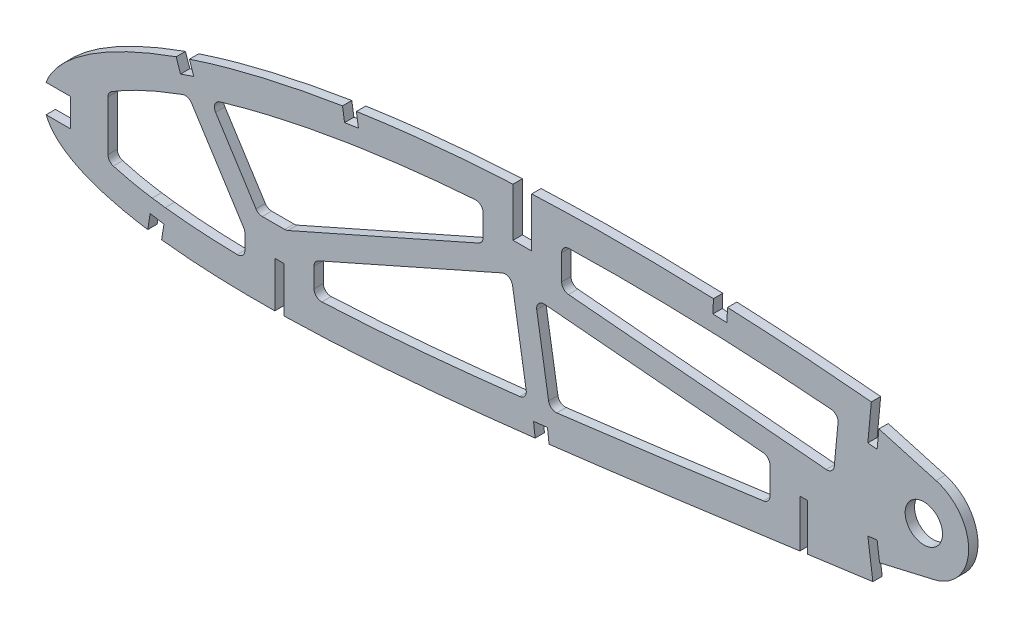
SolidWorks part; units mm, degrees
material "Plywood"
ref_plane "Front Plane" through (0, 0, 0) normal (0, 0, 1) x (1, 0, 0)
ref_plane "Top Plane" through (0, 0, 0) normal (0, 1, 0) x (1, 0, 0)
ref_plane "Right Plane" through (0, 0, 0) normal (1, 0, 0) x (0, 0, -1)
curve "Curve1"
  spline degree 3 poles (452.1031, 0.7048, 0) (452.0685, 0.7262, 0) (451.9301, 0.8117, 0) (451.6183, 1.003, 0) (451.099, 1.3216, 0) (450.372, 1.7653, 0) (449.438, 2.3329, 0) (448.2963, 3.0204, 0) (446.9478, 3.8257, 0) (445.3928, 4.7448, 0) (443.6314, 5.7736, 0) (441.6643, 6.9077, 0) (439.4916, 8.1409, 0) (437.1143, 9.468, 0) (434.5331, 10.8828, 0) (431.7485, 12.3789, 0) (428.7615, 13.9486, 0) (425.5733, 15.5853, 0) (422.1844, 17.2798, 0) (418.5964, 19.0251, 0) (414.8106, 20.8125, 0) (410.8282, 22.6325, 0) (406.6515, 24.4776, 0) (402.2816, 26.3365, 0) (397.7212, 28.201, 0) (392.972, 30.0605, 0) (388.0369, 31.9065, 0) (382.9178, 33.7272, 0) (377.6186, 35.5144, 0) (372.1418, 37.2567, 0) (366.4913, 38.9446, 0) (360.6704, 40.5671, 0) (354.684, 42.1159, 0) (348.5359, 43.5797, 0) (342.2312, 44.9487, 0) (335.775, 46.2147, 0) (329.1727, 47.3651, 0) (322.4425, 48.3989, 0) (315.6929, 49.2588, 0) (308.9571, 50.1023, 0) (302.2314, 50.8946, 0) (295.4235, 51.6533, 0) (288.5399, 52.3742, 0) (281.5875, 53.055, 0) (274.5733, 53.6928, 0) (267.5046, 54.2857, 0) (260.3883, 54.8303, 0) (253.2318, 55.3259, 0) (246.0422, 55.768, 0) (238.8272, 56.1563, 0) (231.5941, 56.4881, 0) (224.3504, 56.7611, 0) (217.1039, 56.9737, 0) (209.862, 57.1238, 0) (202.6326, 57.2105, 0) (195.4232, 57.2315, 0) (188.2416, 57.1863, 0) (181.0954, 57.0734, 0) (173.9924, 56.8912, 0) (166.9401, 56.6395, 0) (159.9462, 56.3182, 0) (153.0184, 55.9248, 0) (146.164, 55.4618, 0) (139.3909, 54.9271, 0) (132.7063, 54.3206, 0) (126.1174, 53.645, 0) (119.6314, 52.8983, 0) (113.2554, 52.0826, 0) (106.9962, 51.1996, 0) (100.8609, 50.2488, 0) (94.8561, 49.2329, 0) (88.9882, 48.153, 0) (83.2635, 47.0122, 0) (77.6882, 45.8109, 0) (72.2682, 44.5525, 0) (67.0092, 43.2395, 0) (61.9167, 41.874, 0) (56.9959, 40.4594, 0) (52.2519, 38.999, 0) (47.6902, 37.4943, 0) (43.3141, 35.951, 0) (39.1291, 34.3702, 0) (35.1384, 32.7568, 0) (31.3466, 31.113, 0) (27.7567, 29.4439, 0) (24.3726, 27.7512, 0) (21.1967, 26.0397, 0) (18.2324, 24.3122, 0) (15.4823, 22.5717, 0) (12.9477, 20.8227, 0) (10.632, 19.0664, 0) (8.5361, 17.307, 0) (6.6613, 15.5474, 0) (5.0102, 13.7886, 0) (3.5829, 12.0339, 0) (2.3811, 10.2847, 0) (1.4051, 8.5424, 0) (0.6571, 6.8085, 0) (0.1363, 5.084, 0) (-0.1488, 3.3712, 0) (-0.2197, 1.669, 0) (-0.0731, 0.5555, 0) (0, 0, 0) knots 0 0 0 0 0.000254 0.001015 0.002283 0.004057 0.006331 0.009105 0.012374 0.016134 0.02038 0.025106 0.030306 0.035972 0.0421 0.048678 0.055702 0.06316 0.071046 0.07935 0.088063 0.097176 0.106678 0.116562 0.126814 0.137428 0.148394 0.1597 0.171338 0.183298 0.19557 0.208144 0.221012 0.234162 0.247587 0.261277 0.275223 0.289414 0.303771 0.317689 0.331784 0.34604 0.360444 0.374983 0.38964 0.404403 0.419257 0.434187 0.449177 0.464215 0.479284 0.49437 0.509458 0.524532 0.539579 0.554583 0.56953 0.584403 0.599191 0.613877 0.628447 0.642889 0.657186 0.671326 0.685294 0.699078 0.712665 0.726043 0.739198 0.752118 0.764792 0.777208 0.789356 0.801224 0.812804 0.824083 0.835055 0.84571 0.856038 0.866034 0.875689 0.884998 0.893953 0.902553 0.910789 0.918661 0.926166 0.933303 0.940071 0.946475 0.952518 0.958205 0.963547 0.968557 0.97325 0.977651 0.981787 0.985694 0.989415 0.993001 0.996508 1 1 1 1
curve "Curve2"
  spline degree 3 poles (0, 0, 0) (0.1161, -0.5481, 0) (0.3488, -1.6467, 0) (0.9811, -3.2283, 0) (1.8173, -4.7487, 0) (2.8749, -6.2038, 0) (4.147, -7.5932, 0) (5.6306, -8.9184, 0) (7.3243, -10.1787, 0) (9.226, -11.3735, 0) (11.3328, -12.5041, 0) (13.6425, -13.5697, 0) (16.1528, -14.5701, 0) (18.8611, -15.5039, 0) (21.764, -16.3724, 0) (24.8588, -17.1737, 0) (28.1419, -17.9088, 0) (31.6103, -18.5759, 0) (35.26, -19.1755, 0) (39.0874, -19.7075, 0) (43.0885, -20.172, 0) (47.2594, -20.5682, 0) (51.596, -20.8969, 0) (56.0938, -21.1583, 0) (60.7487, -21.3533, 0) (65.556, -21.481, 0) (70.5112, -21.5436, 0) (75.6096, -21.5419, 0) (80.8464, -21.4754, 0) (86.2171, -21.3479, 0) (91.7164, -21.1586, 0) (97.3395, -20.9096, 0) (103.0813, -20.6036, 0) (108.9365, -20.2416, 0) (114.9002, -19.8251, 0) (120.967, -19.3576, 0) (127.1315, -18.8401, 0) (133.3883, -18.2757, 0) (139.7319, -17.6673, 0) (146.1567, -17.0167, 0) (152.6572, -16.327, 0) (159.2275, -15.6004, 0) (165.862, -14.8409, 0) (172.5546, -14.0497, 0) (179.2998, -13.2315, 0) (186.0911, -12.3877, 0) (192.923, -11.5217, 0) (199.7891, -10.6375, 0) (206.6832, -9.7349, 0) (213.5994, -8.8205, 0) (220.5311, -7.8935, 0) (227.4721, -6.9586, 0) (234.4161, -6.0188, 0) (241.3564, -5.0743, 0) (248.2868, -4.1291, 0) (255.2009, -3.1857, 0) (262.0918, -2.2442, 0) (268.9535, -1.3094, 0) (275.779, -0.3811, 0) (282.5619, 0.5389, 0) (289.2958, 1.4477, 0) (295.9744, 2.3443, 0) (302.5907, 3.228, 0) (309.138, 4.0992, 0) (315.5119, 4.9314, 0) (321.6955, 5.769, 0) (327.7099, 6.4556, 0) (333.6493, 7.0417, 0) (339.52, 7.5222, 0) (345.315, 7.9041, 0) (351.0275, 8.19, 0) (356.6509, 8.3839, 0) (362.1779, 8.4917, 0) (367.6017, 8.516, 0) (372.9148, 8.4647, 0) (378.1105, 8.3417, 0) (383.1813, 8.1528, 0) (388.1203, 7.9042, 0) (392.9205, 7.6027, 0) (397.5745, 7.2527, 0) (402.076, 6.8625, 0) (406.4179, 6.4377, 0) (410.5937, 5.9833, 0) (414.5972, 5.5086, 0) (418.4221, 5.0169, 0) (422.0625, 4.5163, 0) (425.5126, 4.0117, 0) (428.7669, 3.5097, 0) (431.8204, 3.015, 0) (434.6681, 2.5342, 0) (437.3055, 2.0718, 0) (439.7281, 1.6323, 0) (441.9324, 1.2212, 0) (443.9143, 0.8406, 0) (445.6709, 0.4968, 0) (447.199, 0.1913, 0) (448.4964, -0.0716, 0) (449.5609, -0.2909, 0) (450.3908, -0.463, 0) (450.9844, -0.5881, 0) (451.3411, -0.6626, 0) (451.4997, -0.6964, 0) (451.5393, -0.7048, 0) knots 0 0 0 0 0.003638 0.007293 0.011028 0.014901 0.018963 0.023258 0.027821 0.032679 0.037853 0.043362 0.049215 0.055422 0.061989 0.068918 0.076211 0.083868 0.091887 0.100266 0.109 0.118085 0.127515 0.137285 0.147388 0.157816 0.168563 0.179619 0.190977 0.202627 0.21456 0.226767 0.239236 0.251959 0.264924 0.27812 0.291536 0.30516 0.318981 0.332985 0.347163 0.361499 0.375981 0.390597 0.405333 0.420175 0.43511 0.450124 0.465203 0.480333 0.495501 0.51069 0.525887 0.541078 0.556247 0.571382 0.586466 0.601485 0.616424 0.631269 0.646007 0.660621 0.675098 0.689423 0.703582 0.716908 0.730009 0.742952 0.755726 0.76832 0.780724 0.792927 0.804916 0.816679 0.828204 0.839475 0.850481 0.861208 0.871639 0.881763 0.891564 0.901027 0.910139 0.918884 0.927249 0.935221 0.942785 0.949928 0.956638 0.962904 0.968712 0.974054 0.978918 0.983297 0.98718 0.990561 0.993433 0.995791 0.99763 0.998946 0.999737 1 1 1 1
sketch "Sketch1" plane through (0, 0, 0) normal (0, 0, 1) x (1, 0, 0)
  line L24 (452.1031, 0.7048) -> (456.094, -1.6764)
  line L25 (451.5393, -0.7048) -> (456.094, -1.6764)
  spline S2 degree 3 poles (-2902.3793, -755.52) (63.6454, 63.6466) (-7.9338, 19.0709) (0.9811, -3.2283) (1.8173, -4.7487) (2.8749, -6.2038) (4.147, -7.5932) (5.6306, -8.9184) (7.3243, -10.1787) (9.226, -11.3735) (11.3328, -12.5041) (13.6425, -13.5697) (16.1528, -14.5701) (18.8611, -15.5039) (21.764, -16.3724) (24.8588, -17.1737) (28.1419, -17.9088) (31.6103, -18.5759) (35.26, -19.1755) (39.0874, -19.7075) (43.0885, -20.172) (47.2594, -20.5682) (51.596, -20.8969) (56.0938, -21.1583) (60.7487, -21.3533) (65.556, -21.481) (70.5112, -21.5436) (75.6096, -21.5419) (80.8464, -21.4754) (86.2171, -21.3479) (91.7164, -21.1586) (97.3395, -20.9096) (103.0813, -20.6036) (108.9365, -20.2416) (114.9002, -19.8251) (120.967, -19.3576) (127.1315, -18.8401) (133.3883, -18.2757) (139.7319, -17.6673) (146.1567, -17.0167) (152.6572, -16.327) (159.2275, -15.6004) (165.862, -14.8409) (172.5546, -14.0497) (179.2998, -13.2315) (186.0911, -12.3877) (192.923, -11.5217) (199.7891, -10.6375) (206.6832, -9.7349) (213.5994, -8.8205) (220.5311, -7.8935) (227.4721, -6.9586) (234.4161, -6.0188) (241.3564, -5.0743) (248.2868, -4.1291) (255.2009, -3.1857) (262.0918, -2.2442) (268.9535, -1.3094) (275.779, -0.3811) (282.5619, 0.5389) (289.2958, 1.4477) (295.9744, 2.3443) (302.5907, 3.228) (309.138, 4.0992) (315.5119, 4.9314) (321.6955, 5.769) (327.7099, 6.4556) (333.6493, 7.0417) (339.52, 7.5222) (345.315, 7.9041) (351.0275, 8.19) (356.6509, 8.3839) (362.1779, 8.4917) (367.6017, 8.516) (372.9148, 8.4647) (378.1105, 8.3417) (383.1813, 8.1528) (388.1203, 7.9042) (392.9205, 7.6027) (397.5745, 7.2527) (402.076, 6.8625) (406.4179, 6.4377) (410.5937, 5.9833) (414.5972, 5.5086) (418.4221, 5.0169) (422.0625, 4.5163) (425.5126, 4.0117) (428.7669, 3.5097) (431.8204, 3.015) (434.6681, 2.5342) (437.3055, 2.0718) (439.7281, 1.6323) (441.9324, 1.2212) (443.9143, 0.8406) (445.6709, 0.4968) (447.199, 0.1913) (448.4964, -0.0716) (449.5609, -0.2909) (450.3908, -0.463) (450.9844, -0.5881) (467.4773, -4.0305) (482.2176, -14.7818) (1120.3699, 2922.8002) knots -0.14446 -0.14446 -0.14446 -0.14446 0.003638 0.007293 0.011028 0.014901 0.018963 0.023258 0.027821 0.032679 0.037853 0.043362 0.049215 0.055422 0.061989 0.068918 0.076211 0.083868 0.091887 0.100266 0.109 0.118085 0.127515 0.137285 0.147388 0.157816 0.168563 0.179619 0.190977 0.202627 0.21456 0.226767 0.239236 0.251959 0.264924 0.27812 0.291536 0.30516 0.318981 0.332985 0.347163 0.361499 0.375981 0.390597 0.405333 0.420175 0.43511 0.450124 0.465203 0.480333 0.495501 0.51069 0.525887 0.541078 0.556247 0.571382 0.586466 0.601485 0.616424 0.631269 0.646007 0.660621 0.675098 0.689423 0.703582 0.716908 0.730009 0.742952 0.755726 0.76832 0.780724 0.792927 0.804916 0.816679 0.828204 0.839475 0.850481 0.861208 0.871639 0.881763 0.891564 0.901027 0.910139 0.918884 0.927249 0.935221 0.942785 0.949928 0.956638 0.962904 0.968712 0.974054 0.978918 0.983297 0.98718 0.990561 0.993433 0.995791 0.99763 0.998946 0.999737 1.107215 1.107215 1.107215 1.107215 only from (0, 0) to (451.5393, -0.7048) construction
  spline S3 degree 3 poles (2072.0463, 2524.7843) (479.969, -24.2918) (467.6474, -8.829) (451.6183, 1.003) (451.099, 1.3216) (450.372, 1.7653) (449.438, 2.3329) (448.2963, 3.0204) (446.9478, 3.8257) (445.3928, 4.7448) (443.6314, 5.7736) (441.6643, 6.9077) (439.4916, 8.1409) (437.1143, 9.468) (434.5331, 10.8828) (431.7485, 12.3789) (428.7615, 13.9486) (425.5733, 15.5853) (422.1844, 17.2798) (418.5964, 19.0251) (414.8106, 20.8125) (410.8282, 22.6325) (406.6515, 24.4776) (402.2816, 26.3365) (397.7212, 28.201) (392.972, 30.0605) (388.0369, 31.9065) (382.9178, 33.7272) (377.6186, 35.5144) (372.1418, 37.2567) (366.4913, 38.9446) (360.6704, 40.5671) (354.684, 42.1159) (348.5359, 43.5797) (342.2312, 44.9487) (335.775, 46.2147) (329.1727, 47.3651) (322.4425, 48.3989) (315.6929, 49.2588) (308.9571, 50.1023) (302.2314, 50.8946) (295.4235, 51.6533) (288.5399, 52.3742) (281.5875, 53.055) (274.5733, 53.6928) (267.5046, 54.2857) (260.3883, 54.8303) (253.2318, 55.3259) (246.0422, 55.768) (238.8272, 56.1563) (231.5941, 56.4881) (224.3504, 56.7611) (217.1039, 56.9737) (209.862, 57.1238) (202.6326, 57.2105) (195.4232, 57.2315) (188.2416, 57.1863) (181.0954, 57.0734) (173.9924, 56.8912) (166.9401, 56.6395) (159.9462, 56.3182) (153.0184, 55.9248) (146.164, 55.4618) (139.3909, 54.9271) (132.7063, 54.3206) (126.1174, 53.645) (119.6314, 52.8983) (113.2554, 52.0826) (106.9962, 51.1996) (100.8609, 50.2488) (94.8561, 49.2329) (88.9882, 48.153) (83.2635, 47.0122) (77.6882, 45.8109) (72.2682, 44.5525) (67.0092, 43.2395) (61.9167, 41.874) (56.9959, 40.4594) (52.2519, 38.999) (47.6902, 37.4943) (43.3141, 35.951) (39.1291, 34.3702) (35.1384, 32.7568) (31.3466, 31.113) (27.7567, 29.4439) (24.3726, 27.7512) (21.1967, 26.0397) (18.2324, 24.3122) (15.4823, 22.5717) (12.9477, 20.8227) (10.632, 19.0664) (8.5361, 17.307) (6.6613, 15.5474) (5.0102, 13.7886) (3.5829, 12.0339) (2.3811, 10.2847) (1.4051, 8.5424) (0.6571, 6.8085) (0.1363, 5.084) (-0.1488, 3.3712) (-1.1473, -20.5831) (81.3582, -38.7525) (-2988.6181, -253.0424) knots -0.115084 -0.115084 -0.115084 -0.115084 0.000254 0.001015 0.002283 0.004057 0.006331 0.009105 0.012374 0.016134 0.02038 0.025106 0.030306 0.035972 0.0421 0.048678 0.055702 0.06316 0.071046 0.07935 0.088063 0.097176 0.106678 0.116562 0.126814 0.137428 0.148394 0.1597 0.171338 0.183298 0.19557 0.208144 0.221012 0.234162 0.247587 0.261277 0.275223 0.289414 0.303771 0.317689 0.331784 0.34604 0.360444 0.374983 0.38964 0.404403 0.419257 0.434187 0.449177 0.464215 0.479284 0.49437 0.509458 0.524532 0.539579 0.554583 0.56953 0.584403 0.599191 0.613877 0.628447 0.642889 0.657186 0.671326 0.685294 0.699078 0.712665 0.726043 0.739198 0.752118 0.764792 0.777208 0.789356 0.801224 0.812804 0.824083 0.835055 0.84571 0.856038 0.866034 0.875689 0.884998 0.893953 0.902553 0.910789 0.918661 0.926166 0.933303 0.940071 0.946475 0.952518 0.958205 0.963547 0.968557 0.97325 0.977651 0.981787 0.985694 0.989415 0.993001 0.996508 1.138367 1.138367 1.138367 1.138367 only from (452.1031, 0.7048) to (0, 0) construction
  spline S4 degree 3 poles (0, 0) (0.1161, -0.5481) (0.3488, -1.6467) (0.9811, -3.2283) (1.8173, -4.7487) (2.8749, -6.2038) (4.147, -7.5932) (5.6306, -8.9184) (7.3243, -10.1787) (9.226, -11.3735) (11.3328, -12.5041) (13.6425, -13.5697) (16.1528, -14.5701) (18.8611, -15.5039) (21.764, -16.3724) (24.8588, -17.1737) (28.1419, -17.9088) (31.6103, -18.5759) (35.26, -19.1755) (39.0874, -19.7075) (43.0885, -20.172) (47.2594, -20.5682) (51.596, -20.8969) (56.0938, -21.1583) (60.7487, -21.3533) (65.556, -21.481) (70.5112, -21.5436) (75.6096, -21.5419) (80.8464, -21.4754) (86.2171, -21.3479) (91.7164, -21.1586) (97.3395, -20.9096) (103.0813, -20.6036) (108.9365, -20.2416) (114.9002, -19.8251) (120.967, -19.3576) (127.1315, -18.8401) (133.3883, -18.2757) (139.7319, -17.6673) (146.1567, -17.0167) (152.6572, -16.327) (159.2275, -15.6004) (165.862, -14.8409) (172.5546, -14.0497) (179.2998, -13.2315) (186.0911, -12.3877) (192.923, -11.5217) (199.7891, -10.6375) (206.6832, -9.7349) (213.5994, -8.8205) (220.5311, -7.8935) (227.4721, -6.9586) (234.4161, -6.0188) (241.3564, -5.0743) (248.2868, -4.1291) (255.2009, -3.1857) (262.0918, -2.2442) (268.9535, -1.3094) (275.779, -0.3811) (282.5619, 0.5389) (289.2958, 1.4477) (295.9744, 2.3443) (302.5907, 3.228) (309.138, 4.0992) (315.5119, 4.9314) (321.6955, 5.769) (327.7099, 6.4556) (333.6493, 7.0417) (339.52, 7.5222) (345.315, 7.9041) (351.0275, 8.19) (356.6509, 8.3839) (362.1779, 8.4917) (367.6017, 8.516) (372.9148, 8.4647) (378.1105, 8.3417) (383.1813, 8.1528) (388.1203, 7.9042) (392.9205, 7.6027) (397.5745, 7.2527) (402.076, 6.8625) (406.4179, 6.4377) (410.5937, 5.9833) (414.5972, 5.5086) (418.4221, 5.0169) (422.0625, 4.5163) (425.5126, 4.0117) (428.7669, 3.5097) (431.8204, 3.015) (434.6681, 2.5342) (437.3055, 2.0718) (439.7281, 1.6323) (441.9324, 1.2212) (443.9143, 0.8406) (445.6709, 0.4968) (447.199, 0.1913) (448.4964, -0.0716) (449.5609, -0.2909) (450.3908, -0.463) (450.9844, -0.5881) (451.3411, -0.6626) (451.4997, -0.6964) (451.5393, -0.7048) knots 0 0 0 0 0.003638 0.007293 0.011028 0.014901 0.018963 0.023258 0.027821 0.032679 0.037853 0.043362 0.049215 0.055422 0.061989 0.068918 0.076211 0.083868 0.091887 0.100266 0.109 0.118085 0.127515 0.137285 0.147388 0.157816 0.168563 0.179619 0.190977 0.202627 0.21456 0.226767 0.239236 0.251959 0.264924 0.27812 0.291536 0.30516 0.318981 0.332985 0.347163 0.361499 0.375981 0.390597 0.405333 0.420175 0.43511 0.450124 0.465203 0.480333 0.495501 0.51069 0.525887 0.541078 0.556247 0.571382 0.586466 0.601485 0.616424 0.631269 0.646007 0.660621 0.675098 0.689423 0.703582 0.716908 0.730009 0.742952 0.755726 0.76832 0.780724 0.792927 0.804916 0.816679 0.828204 0.839475 0.850481 0.861208 0.871639 0.881763 0.891564 0.901027 0.910139 0.918884 0.927249 0.935221 0.942785 0.949928 0.956638 0.962904 0.968712 0.974054 0.978918 0.983297 0.98718 0.990561 0.993433 0.995791 0.99763 0.998946 0.999737 1 1 1 1
  spline S5 degree 3 poles (452.1031, 0.7048) (452.0685, 0.7262) (451.9301, 0.8117) (451.6183, 1.003) (451.099, 1.3216) (450.372, 1.7653) (449.438, 2.3329) (448.2963, 3.0204) (446.9478, 3.8257) (445.3928, 4.7448) (443.6314, 5.7736) (441.6643, 6.9077) (439.4916, 8.1409) (437.1143, 9.468) (434.5331, 10.8828) (431.7485, 12.3789) (428.7615, 13.9486) (425.5733, 15.5853) (422.1844, 17.2798) (418.5964, 19.0251) (414.8106, 20.8125) (410.8282, 22.6325) (406.6515, 24.4776) (402.2816, 26.3365) (397.7212, 28.201) (392.972, 30.0605) (388.0369, 31.9065) (382.9178, 33.7272) (377.6186, 35.5144) (372.1418, 37.2567) (366.4913, 38.9446) (360.6704, 40.5671) (354.684, 42.1159) (348.5359, 43.5797) (342.2312, 44.9487) (335.775, 46.2147) (329.1727, 47.3651) (322.4425, 48.3989) (315.6929, 49.2588) (308.9571, 50.1023) (302.2314, 50.8946) (295.4235, 51.6533) (288.5399, 52.3742) (281.5875, 53.055) (274.5733, 53.6928) (267.5046, 54.2857) (260.3883, 54.8303) (253.2318, 55.3259) (246.0422, 55.768) (238.8272, 56.1563) (231.5941, 56.4881) (224.3504, 56.7611) (217.1039, 56.9737) (209.862, 57.1238) (202.6326, 57.2105) (195.4232, 57.2315) (188.2416, 57.1863) (181.0954, 57.0734) (173.9924, 56.8912) (166.9401, 56.6395) (159.9462, 56.3182) (153.0184, 55.9248) (146.164, 55.4618) (139.3909, 54.9271) (132.7063, 54.3206) (126.1174, 53.645) (119.6314, 52.8983) (113.2554, 52.0826) (106.9962, 51.1996) (100.8609, 50.2488) (94.8561, 49.2329) (88.9882, 48.153) (83.2635, 47.0122) (77.6882, 45.8109) (72.2682, 44.5525) (67.0092, 43.2395) (61.9167, 41.874) (56.9959, 40.4594) (52.2519, 38.999) (47.6902, 37.4943) (43.3141, 35.951) (39.1291, 34.3702) (35.1384, 32.7568) (31.3466, 31.113) (27.7567, 29.4439) (24.3726, 27.7512) (21.1967, 26.0397) (18.2324, 24.3122) (15.4823, 22.5717) (12.9477, 20.8227) (10.632, 19.0664) (8.5361, 17.307) (6.6613, 15.5474) (5.0102, 13.7886) (3.5829, 12.0339) (2.3811, 10.2847) (1.4051, 8.5424) (0.6571, 6.8085) (0.1363, 5.084) (-0.1488, 3.3712) (-0.2197, 1.669) (-0.0731, 0.5555) (0, 0) knots 0 0 0 0 0.000254 0.001015 0.002283 0.004057 0.006331 0.009105 0.012374 0.016134 0.02038 0.025106 0.030306 0.035972 0.0421 0.048678 0.055702 0.06316 0.071046 0.07935 0.088063 0.097176 0.106678 0.116562 0.126814 0.137428 0.148394 0.1597 0.171338 0.183298 0.19557 0.208144 0.221012 0.234162 0.247587 0.261277 0.275223 0.289414 0.303771 0.317689 0.331784 0.34604 0.360444 0.374983 0.38964 0.404403 0.419257 0.434187 0.449177 0.464215 0.479284 0.49437 0.509458 0.524532 0.539579 0.554583 0.56953 0.584403 0.599191 0.613877 0.628447 0.642889 0.657186 0.671326 0.685294 0.699078 0.712665 0.726043 0.739198 0.752118 0.764792 0.777208 0.789356 0.801224 0.812804 0.824083 0.835055 0.84571 0.856038 0.866034 0.875689 0.884998 0.893953 0.902553 0.910789 0.918661 0.926166 0.933303 0.940071 0.946475 0.952518 0.958205 0.963547 0.968557 0.97325 0.977651 0.981787 0.985694 0.989415 0.993001 0.996508 1 1 1 1
extrude "Boss-Extrude1" add sketch "Sketch1" along normal blind 3.175
sketch "Sketch2" plane through (0, 0, 0) normal (0, 0, -1) x (-1, 0, 0)
  line L0 (-81.6491, -6.0107) -> (-78.4741, -6.0107)
  line L1 (-81.6491, -20.9228) -> (-81.6491, -22.4869)
  line L2 (-259.4491, 13.2207) -> (-259.4491, -2.6526)
  line L4 (-81.6491, -22.4869) -> (-78.4741, -21.7048)
  line L5 (-78.4741, -21.7048) -> (-78.4741, -20.9228)
  line L7 (-165.7866, 56.5935) -> (-165.7866, 39.7629)
  line L8 (-165.7866, 39.7629) -> (-159.4366, 39.7629)
  line L9 (-165.7866, 56.5935) -> (-165.7866, 58.5208)
  line L10 (-81.6491, -6.0107) -> (-81.6491, -20.9228)
  line L12 (-165.7866, 58.5208) -> (-159.4366, 57.5572)
  line L13 (-159.4366, 57.5572) -> (-159.4366, 56.5935)
  line L14 (-78.4741, -6.0107) -> (-78.4741, -20.9228)
  line L16 (-259.4491, 13.2207) -> (-256.9091, 13.2207)
  line L17 (-259.4491, -2.6526) -> (-259.4491, -5.0698)
  line L19 (-159.4366, 56.5935) -> (-159.4366, 39.7629)
  line L20 (-259.4491, -5.0698) -> (-256.9091, -3.8612)
  line L21 (-256.9091, -3.8612) -> (-256.9091, -2.6526)
  line L22 (-256.9091, 13.2207) -> (-256.9091, -2.6526)
extrude "Cut-Extrude1" cut sketch "Sketch2" against normal blind 7.62
sketch "Sketch3" plane through (0, 0, 0) normal (0, 0, -1) x (-1, 0, 0)
  circle A1 centre (-299.0384, 26.2554) radius 6.35
extrude "Cut-Extrude2" cut sketch "Sketch3" against normal blind 7.62
sketch "Sketch4" plane through (0, 0, 3.175) normal (0, 0, 1) x (1, 0, 0)
  line L0 (283.1634, 40.1032) -> (284.3809, 52.7385)
  line L1 (283.1634, 40.1032) -> (284.3809, 52.7385)
  line L2 (284.8624, 0.8345) -> (283.1634, 13.4207)
  line L3 (284.8624, 0.8345) -> (283.1634, 13.4207)
  line L4 (283.1634, 13.4207) -> (280.017, 12.9956)
  line L5 (283.1634, 13.4207) -> (280.017, 12.9956)
  line L6 (280.003, 40.404) -> (283.1634, 40.1032)
  line L7 (280.003, 40.404) -> (283.1634, 40.1032)
  line L8 (280.017, 12.9956) -> (281.7174, 0.4099)
  line L9 (280.017, 12.9956) -> (281.7174, 0.4099)
  line L10 (281.2061, 53.046) -> (280.003, 40.404)
  line L11 (281.2061, 53.046) -> (280.003, 40.404)
  line L12 (227.543, 56.7883) -> (227.3611, 52.0373)
  line L13 (227.543, 56.7883) -> (227.3611, 52.0373)
  line L14 (101.4521, 50.4601) -> (102.1913, 45.7722)
  line L15 (101.4521, 50.4601) -> (102.1913, 45.7722)
  line L16 (44.909, 36.6556) -> (46.4387, 32.1792)
  line L17 (44.909, 36.6556) -> (46.4387, 32.1792)
  line L18 (166.4044, -10.0397) -> (166.9563, -14.7725)
  line L19 (166.4044, -10.0397) -> (166.9563, -14.7725)
  line L20 (36.1137, -14.0525) -> (35.373, -18.771)
  line L21 (36.1137, -14.0525) -> (35.373, -18.771)
  line L22 (40.8104, -14.7911) -> (36.1137, -14.0525)
  line L23 (40.8104, -14.7911) -> (36.1137, -14.0525)
  line L24 (171.134, -9.4806) -> (166.4044, -10.0397)
  line L25 (171.134, -9.4806) -> (166.4044, -10.0397)
  line L26 (50.9453, 33.7189) -> (49.4124, 38.2061)
  line L27 (50.9453, 33.7189) -> (49.4124, 38.2061)
  line L28 (40.0562, -19.5592) -> (40.8104, -14.7911)
  line L29 (40.0562, -19.5592) -> (40.8104, -14.7911)
  line L30 (106.9007, 46.4815) -> (106.1899, 51.2009)
  line L31 (106.9007, 46.4815) -> (106.1899, 51.2009)
  line L32 (232.1192, 51.8391) -> (232.3281, 56.5914)
  line L33 (232.1192, 51.8391) -> (232.3281, 56.5914)
  line L34 (171.6935, -14.2138) -> (171.134, -9.4806)
  line L35 (171.6935, -14.2138) -> (171.134, -9.4806)
  line L36 (227.3611, 52.0373) -> (232.1192, 51.8391)
  line L37 (227.3611, 52.0373) -> (232.1192, 51.8391)
  line L38 (102.1913, 45.7722) -> (106.9007, 46.4815)
  line L39 (102.1913, 45.7722) -> (106.9007, 46.4815)
  line L40 (-0.4483, -2.6341) -> (9.0767, -2.6341)
  line L41 (-0.4483, -2.6341) -> (9.0767, -2.6341)
  line L42 (-0.4483, 6.8909) -> (9.0767, 6.8909)
  line L43 (-0.4483, 6.8909) -> (9.0767, 6.8909)
  line L44 (9.0767, -2.6341) -> (9.0767, 6.8909)
  line L45 (9.0767, -2.6341) -> (9.0767, 6.8909)
  line L46 (46.4387, 32.1792) -> (50.9453, 33.7189)
  line L47 (46.4387, 32.1792) -> (50.9453, 33.7189)
  line L48 (281.7174, 0.4099) -> (282.0892, -2.3425)
  line L49 (282.0892, -2.3425) -> (285.2356, -1.9174)
  line L50 (285.2356, -1.9174) -> (284.8624, 0.8345)
  line L51 (281.2061, 53.046) -> (281.5903, 57.0828)
  line L52 (281.5903, 57.0828) -> (284.7703, 56.7802)
  line L53 (284.7703, 56.7802) -> (284.3809, 52.7385)
  line L54 (227.543, 56.7883) -> (232.3281, 56.5914)
  line L55 (101.4521, 50.4601) -> (106.1899, 51.2009)
  line L56 (44.909, 36.6556) -> (49.4124, 38.2061)
  line L57 (-0.4483, -2.6341) -> (-0.4483, 6.8909)
  line L58 (35.373, -18.771) -> (34.8729, -21.9571)
  line L59 (34.8729, -21.9571) -> (39.5676, -22.6941)
  line L60 (39.5676, -22.6941) -> (40.0562, -19.5592)
  line L61 (166.9563, -14.7725) -> (171.6935, -14.2138)
  line L62 (283.7722, 46.4209) -> (303.193, 40.9182)
  line L63 (284.0129, 7.1276) -> (302.4805, 11.4092)
  line L64 (284.3809, 52.7385) -> (466.0882, 52.7385)
  line L65 (466.0882, 52.7385) -> (466.0882, -18.771)
  line L66 (466.0882, -18.771) -> (284.8624, 0.8345)
  circle A0 centre (299.0384, 26.2554) radius 6.35 construction
  circle A1 centre (299.0384, 26.2554) radius 6.35
  circle A2 centre (299.0384, 26.2554) radius 15.24
  dimension "D1" = 30.48
extrude "Cut-Extrude3" cut sketch "Sketch4" against normal through all
sketch "Sketch5" plane through (0, 0, 3.175) normal (0, 0, 1) x (1, 0, 0)
  line L0 (36.8297, -9.1216) -> (41.2489, -9.7235)
  line L1 (44.954, 36.5241) -> (49.458, 38.0725) construction
  line L2 (103.0835, 40.3016) -> (107.7147, 41.0203)
  line L3 (227.1599, 46.4854) -> (231.8893, 46.2967)
  line L4 (165.7688, -4.6187) -> (170.4819, -4.0617)
  line L5 (169.5966, 39.7629) -> (169.5966, 56.2793)
  line L6 (68.3141, -21.5029) -> (68.3141, 4.1493)
  line L7 (68.3141, 4.1493) -> (91.8091, 4.1493)
  line L8 (91.8091, 4.1493) -> (91.8091, -21.4504)
  line L9 (175.9466, 56.5794) -> (175.9466, 29.6029)
  line L10 (175.9466, 29.6029) -> (149.2766, 29.6029)
  line L11 (149.2766, 29.6029) -> (149.2766, 56.2793)
  line L12 (246.7491, -2.9522) -> (246.7491, 23.3807)
  line L13 (246.7491, 23.3807) -> (269.6091, 23.3807)
  line L14 (269.6091, 23.3807) -> (269.6091, -2.6054)
  line L15 (268.177, 23.3807) -> (271.0953, 54.0451)
  line L16 (269.8887, 41.3666) -> (271.0953, 54.0451) construction
  line L17 (47.206, 37.2983) -> (68.3141, 4.1493) construction
  line L18 (91.8091, 4.1493) -> (149.2766, 29.6029) construction
  line L19 (168.1254, -4.3402) -> (162.6116, 29.6029) construction
  line L20 (246.7491, 23.3807) -> (175.9466, 29.6029) construction
  line L21 (44.5484, 34.3785) -> (68.3141, -2.9442)
  line L22 (91.8091, -0.0177) -> (158.6846, 29.6029)
  line L23 (171.9123, -3.8905) -> (166.3723, 30.2138)
  line L24 (268.3602, 25.3062) -> (175.9466, 33.4276)
  line L25 (50.4197, 39.3447) -> (72.8309, 4.1493)
  line L26 (82.4011, 4.1493) -> (149.2766, 33.7699)
  line L27 (164.3647, -4.9511) -> (158.7516, 29.6029)
  line L28 (246.7491, 19.5561) -> (166.9646, 26.5675)
  line L29 (43.9922, 35.2519) -> (65.1003, 2.1029) construction
  line L30 (50.4197, 39.3447) -> (71.5278, 6.1957) construction
  line L31 (90.2661, 7.6329) -> (147.7336, 33.0865) construction
  line L32 (93.352, 0.6657) -> (150.8195, 26.1193) construction
  line L33 (246.4155, 19.5854) -> (175.613, 25.8075) construction
  line L34 (247.0826, 27.1761) -> (176.2801, 33.3982) construction
  line L35 (164.3647, -4.9511) -> (158.8509, 28.992) construction
  line L36 (9.0767, 6.8909) -> (9.0767, -2.6341)
  line L37 (9.0767, -2.6341) -> (0.7554, -2.6341)
  line L38 (35.3108, -19.1674) -> (36.1137, -14.0525)
  line L39 (36.1137, -14.0525) -> (40.8104, -14.7911)
  line L40 (40.8104, -14.7911) -> (40.0562, -19.5592)
  line L41 (40.0562, -19.5592) -> (40.0174, -19.8086)
  line L42 (78.4741, -21.5029) -> (78.4741, -6.0107)
  line L43 (78.4741, -6.0107) -> (81.6491, -6.0107)
  line L44 (81.6491, -6.0107) -> (81.6491, -21.4504)
  line L45 (166.949, -14.7099) -> (166.4044, -10.0397)
  line L46 (166.4044, -10.0397) -> (171.134, -9.4806)
  line L47 (171.134, -9.4806) -> (171.686, -14.1501)
  line L48 (256.9091, -2.9522) -> (256.9091, 13.2207)
  line L49 (256.9091, 13.2207) -> (259.4491, 13.2207)
  line L50 (259.4491, 13.2207) -> (259.4491, -2.6054)
  line L51 (281.7155, 0.4236) -> (280.017, 12.9956)
  line L52 (280.017, 12.9956) -> (283.1634, 13.4207)
  line L53 (283.1634, 13.4207) -> (284.0129, 7.1276)
  line L54 (284.0129, 7.1276) -> (302.4805, 11.4092)
  line L55 (303.193, 40.9182) -> (283.7722, 46.4209)
  line L56 (283.7722, 46.4209) -> (283.1634, 40.1032)
  line L57 (283.1634, 40.1032) -> (280.003, 40.404)
  line L58 (280.003, 40.404) -> (281.2096, 53.0825)
  line L59 (48.3594, 26.9518) -> (52.6619, 28.4309)
  line L60 (21.7767, 14.5224) -> (21.7767, -5.7474)
  line L62 (165.7866, 56.5794) -> (165.7866, 39.7629)
  line L63 (165.7866, 39.7629) -> (159.4366, 39.7629)
  line L64 (159.4366, 39.7629) -> (159.4366, 56.2793)
  line L71 (0.7247, 6.8909) -> (9.0767, 6.8909)
  line L72 (9.0767, 6.8909) -> (9.0767, -2.6341)
  line L73 (9.0767, -2.6341) -> (0.7554, -2.6341)
  line L74 (35.3108, -19.1674) -> (36.1137, -14.0525)
  line L75 (36.1137, -14.0525) -> (40.8104, -14.7911)
  line L76 (40.8104, -14.7911) -> (40.0562, -19.5592)
  line L77 (40.0562, -19.5592) -> (40.0174, -19.8086)
  line L78 (78.4741, -21.5029) -> (78.4741, -6.0107)
  line L79 (78.4741, -6.0107) -> (81.6491, -6.0107)
  line L80 (81.6491, -6.0107) -> (81.6491, -21.4504)
  line L81 (166.949, -14.7099) -> (166.4044, -10.0397)
  line L82 (166.4044, -10.0397) -> (171.134, -9.4806)
  line L83 (171.134, -9.4806) -> (171.686, -14.1501)
  line L84 (256.9091, -2.9522) -> (256.9091, 13.2207)
  line L85 (256.9091, 13.2207) -> (259.4491, 13.2207)
  line L86 (259.4491, 13.2207) -> (259.4491, -2.6054)
  line L87 (281.7155, 0.4236) -> (280.017, 12.9956)
  line L88 (280.017, 12.9956) -> (283.1634, 13.4207)
  line L89 (283.1634, 13.4207) -> (284.0129, 7.1276)
  line L90 (284.0129, 7.1276) -> (302.4805, 11.4092)
  line L91 (303.193, 40.9182) -> (283.7722, 46.4209)
  line L92 (283.7722, 46.4209) -> (283.1634, 40.1032)
  line L93 (283.1634, 40.1032) -> (280.003, 40.404)
  line L94 (280.003, 40.404) -> (281.2096, 53.0825)
  line L98 (165.7866, 56.5794) -> (165.7866, 39.7629)
  line L99 (165.7866, 39.7629) -> (159.4366, 39.7629)
  line L100 (159.4366, 39.7629) -> (159.4366, 56.2793)
  line L107 (0.7247, 6.8909) -> (9.0767, 6.8909)
  line L108 (171.8861, -3.7293) -> (166.3723, 30.2138) construction
  line L136 (232.3218, 56.4475) -> (232.1192, 51.8391)
  line L137 (232.3218, 56.4475) -> (232.1192, 51.8391)
  line L138 (232.1192, 51.8391) -> (227.3611, 52.0373)
  line L139 (232.1192, 51.8391) -> (227.3611, 52.0373)
  line L140 (227.3611, 52.0373) -> (227.5373, 56.6384)
  line L141 (227.3611, 52.0373) -> (227.5373, 56.6384)
  line L142 (106.2099, 51.0682) -> (106.9007, 46.4815)
  line L143 (106.2099, 51.0682) -> (106.9007, 46.4815)
  line L144 (106.9007, 46.4815) -> (102.1913, 45.7722)
  line L145 (106.9007, 46.4815) -> (102.1913, 45.7722)
  line L146 (102.1913, 45.7722) -> (101.4722, 50.3331)
  line L147 (102.1913, 45.7722) -> (101.4722, 50.3331)
  line L148 (49.458, 38.0725) -> (50.9453, 33.7189)
  line L149 (49.458, 38.0725) -> (50.9453, 33.7189)
  line L150 (50.9453, 33.7189) -> (46.4387, 32.1792)
  line L151 (50.9453, 33.7189) -> (46.4387, 32.1792)
  line L152 (46.4387, 32.1792) -> (44.954, 36.5241)
  line L153 (46.4387, 32.1792) -> (44.954, 36.5241)
  arc A1 (302.4805, 11.4092) -> (303.193, 40.9182) centre (299.0384, 26.2554) ccw
  arc A2 (302.4805, 11.4092) -> (303.193, 40.9182) centre (299.0384, 26.2554) ccw
  arc A3 (155.7389, 28.2982) -> (159.2747, 26.3831) centre (156.7675, 25.9758) cw
  spline S0 degree 1 poles (227.1599, 46.4854) (166.218, 46.4286) knots 0 0 1 1 construction
  spline S1 degree 3 poles (227.1599, 46.4854) (222.0775, 46.6743) (211.9065, 46.9628) (196.6607, 47.1116) (181.4242, 46.9602) (171.2863, 46.644) (166.218, 46.4286) knots 0.487735 0.487735 0.487735 0.487735 0.519862 0.551988 0.584115 0.616241 0.616241 0.616241 0.616241
  spline S2 degree 1 poles (103.0835, 40.3016) (52.6619, 28.4309) knots 0 0 1 1 construction
  spline S3 degree 3 poles (103.0835, 40.3016) (98.7884, 39.6117) (90.2072, 38.101) (77.4851, 35.416) (64.9143, 32.2473) (56.7277, 29.782) (52.6619, 28.4309) knots 0.750752 0.750752 0.750752 0.750752 0.778577 0.806402 0.834226 0.862051 0.862051 0.862051 0.862051
  spline S4 degree 1 poles (159.9656, 46.133) (107.7147, 41.0203) knots 0 0 1 1 construction
  spline S5 degree 3 poles (159.9656, 46.133) (155.5848, 45.9046) (146.8227, 45.3584) (133.729, 44.2514) (120.6796, 42.8345) (112.0321, 41.6668) (107.7147, 41.0203) knots 0.629467 0.629467 0.629467 0.629467 0.657295 0.685123 0.71295 0.740778 0.740778 0.740778 0.740778
  spline S6 degree 1 poles (48.3594, 26.9518) (10.2443, 3.3408) knots 0 0 1 1 construction
  spline S7 degree 3 poles (48.3594, 26.9518) (46.3271, 26.2288) (42.2727, 24.7134) (36.3512, 22.2504) (30.6067, 19.5659) (26.2002, 17.2158) (22.875, 15.2356) (20.9323, 13.9851) (18.3696, 12.2116) (15.9898, 10.3645) (13.6295, 8.1613) (12.2956, 6.6705) (11.4374, 5.5303) (10.9076, 4.7161) (10.5723, 4.0993) (10.3642, 3.6463) (10.2835, 3.4459) (10.2443, 3.3408) knots 0.87196 0.87196 0.87196 0.87196 0.886143 0.900325 0.914508 0.928691 0.934469 0.941561 0.945106 0.957057 0.964148 0.97124 0.974785 0.978331 0.981877 0.98365 0.985422 0.985422 0.985422 0.985422
  spline S8 degree 1 poles (280.2583, 42.9671) (231.8893, 46.2967) knots 0 0 1 1 construction
  spline S9 degree 3 poles (280.2583, 42.9671) (276.2333, 43.3456) (268.1781, 44.0543) (256.0871, 44.9675) (243.9908, 45.7255) (235.9242, 46.1248) (231.8893, 46.2967) knots 0.375811 0.375811 0.375811 0.375811 0.401301 0.426792 0.452283 0.477773 0.477773 0.477773 0.477773
  spline S10 degree 3 poles (2996.1949, -120.1681) (68.8079, 100.486) (-13.8364, 23.7132) (1.8173, -4.7487) (2.8749, -6.2038) (4.147, -7.5932) (5.6306, -8.9184) (7.3243, -10.1787) (9.226, -11.3735) (11.3328, -12.5041) (13.6425, -13.5697) (16.1528, -14.5701) (18.8611, -15.5039) (21.764, -16.3724) (24.8588, -17.1737) (28.1419, -17.9088) (31.6103, -18.5759) (187.4628, -44.1824) (378.1311, 168.904) (-528.578, -2946.2693) knots -0.195944 -0.195944 -0.195944 -0.195944 0.007293 0.011028 0.014901 0.018963 0.023258 0.027821 0.032679 0.037853 0.043362 0.049215 0.055422 0.061989 0.068918 0.076211 0.083868 0.091887 1.103396 1.103396 1.103396 1.103396 only from (0.7554, -2.6341) to (35.3108, -19.1674)
  spline S11 degree 3 poles (383.1746, 2938.9534) (-241.4033, 187.7044) (-107.1925, -5.8964) (47.2594, -20.5682) (51.596, -20.8969) (56.0938, -21.1583) (60.7487, -21.3533) (65.556, -21.481) (70.5112, -21.5436) (311.0354, -21.4625) (548.5051, 183.1092) (528.914, -2934.251) knots -0.881539 -0.881539 -0.881539 -0.881539 0.109 0.118085 0.127515 0.137285 0.147388 0.157816 0.168563 0.179619 1.722211 1.722211 1.722211 1.722211 only from (40.0174, -19.8086) to (78.4741, -21.5029)
  spline S12 degree 3 poles (-426.1142, 2866.6667) (-483.7062, 195.974) (-193.473, -30.9789) (91.7164, -21.1586) (97.3395, -20.9096) (103.0813, -20.6036) (108.9365, -20.2416) (114.9002, -19.8251) (120.967, -19.3576) (127.1315, -18.8401) (133.3883, -18.2757) (139.7319, -17.6673) (146.1567, -17.0167) (152.6572, -16.327) (159.2275, -15.6004) (520.5855, 25.7688) (867.324, 173.6054) (1500.4861, -2567.2227) knots -1.62925 -1.62925 -1.62925 -1.62925 0.202627 0.21456 0.226767 0.239236 0.251959 0.264924 0.27812 0.291536 0.30516 0.318981 0.332985 0.347163 0.361499 0.375981 2.712882 2.712882 2.712882 2.712882 only from (81.6491, -21.4504) to (166.949, -14.7099)
  spline S13 degree 3 poles (-1113.2645, 2591.5657) (-508.2196, -17.6704) (-160.9259, -54.503) (179.2998, -13.2315) (186.0911, -12.3877) (192.923, -11.5217) (199.7891, -10.6375) (206.6832, -9.7349) (213.5994, -8.8205) (220.5311, -7.8935) (227.4721, -6.9586) (234.4161, -6.0188) (241.3564, -5.0743) (248.2868, -4.1291) (623.8921, 47.1201) (996.4723, 103.2879) (1726.8806, -2479.8008) knots -1.808967 -1.808967 -1.808967 -1.808967 0.390597 0.405333 0.420175 0.43511 0.450124 0.465203 0.480333 0.495501 0.51069 0.525887 0.541078 0.556247 0.571382 3.006756 3.006756 3.006756 3.006756 only from (171.686, -14.1501) to (256.9091, -2.9522)
  spline S14 degree 3 poles (-1211.7865, 2472.8735) (-479.9258, -114.9429) (-107.4015, -52.584) (268.9535, -1.3094) (719.3362, 59.9474) (1169.6953, 104.2388) (1946.6575, -2299.7384) knots -1.854107 -1.854107 -1.854107 -1.854107 0.586466 0.601485 0.616424 3.542851 3.542851 3.542851 3.542851 only from (259.4491, -2.6054) to (281.7155, 0.4236)
  spline S15 degree 3 poles (263.494, -2257.8705) (1773.0722, -1014.4627) (1062.3939, -12.3862) (267.5046, 54.2857) (260.3883, 54.8303) (253.2318, 55.3259) (246.0422, 55.768) (-203.8595, 79.9809) (-667.8281, -225.5032) (-730.3561, -2616.6816) knots -4.559436 -4.559436 -4.559436 -4.559436 0.38964 0.404403 0.419257 0.434187 0.449177 0.464215 3.246291 3.246291 3.246291 3.246291 only from (281.2096, 53.0825) to (232.3218, 56.4475)
  spline S17 degree 3 poles (-285.9086, -2382.4887) (1412.7105, -719.3634) (753.9551, 96.5234) (146.164, 55.4618) (139.3909, 54.9271) (132.7063, 54.3206) (126.1174, 53.645) (119.6314, 52.8983) (113.2554, 52.0826) (-208.7209, 6.6609) (-478.8724, -374.5862) (309.958, -2845.5265) knots -3.130783 -3.130783 -3.130783 -3.130783 0.642889 0.657186 0.671326 0.685294 0.699078 0.712665 0.726043 0.739198 2.742124 2.742124 2.742124 2.742124 only from (159.4366, 56.2793) to (106.2099, 51.0682)
  spline S20 degree 3 poles (0.7554, -2.6341) (0.8346, -2.8252) (1.1527, -3.5402) (1.8173, -4.7487) (2.8749, -6.2038) (4.147, -7.5932) (5.6306, -8.9184) (7.3243, -10.1787) (9.226, -11.3735) (11.3328, -12.5041) (13.6425, -13.5697) (16.1528, -14.5701) (18.8611, -15.5039) (21.764, -16.3724) (24.8588, -17.1737) (28.1419, -17.9088) (31.6103, -18.5759) (34.0231, -18.9723) (35.2764, -19.1622) (35.3108, -19.1674) knots 0.005949 0.005949 0.005949 0.005949 0.007293 0.011028 0.014901 0.018963 0.023258 0.027821 0.032679 0.037853 0.043362 0.049215 0.055422 0.061989 0.068918 0.076211 0.083868 0.091887 0.092113 0.092113 0.092113 0.092113
  spline S21 degree 3 poles (40.0174, -19.8086) (41.0228, -19.9313) (43.4171, -20.2032) (47.2594, -20.5682) (51.596, -20.8969) (56.0938, -21.1583) (60.7487, -21.3533) (65.556, -21.481) (70.5112, -21.5436) (74.8337, -21.5421) (77.5038, -21.5157) (78.4741, -21.5029) knots 0.102412 0.102412 0.102412 0.102412 0.109 0.118085 0.127515 0.137285 0.147388 0.157816 0.168563 0.179619 0.185931 0.185931 0.185931 0.185931
  spline S22 degree 3 poles (81.6491, -21.4504) (83.1573, -21.4203) (86.4995, -21.3382) (91.7164, -21.1586) (97.3395, -20.9096) (103.0813, -20.6036) (108.9365, -20.2416) (114.9002, -19.8251) (120.967, -19.3576) (127.1315, -18.8401) (133.3883, -18.2757) (139.7319, -17.6673) (146.1567, -17.0167) (152.6572, -16.327) (159.2275, -15.6004) (163.9988, -15.0542) (166.5797, -14.7531) (166.949, -14.7099) knots 0.192815 0.192815 0.192815 0.192815 0.202627 0.21456 0.226767 0.239236 0.251959 0.264924 0.27812 0.291536 0.30516 0.318981 0.332985 0.347163 0.361499 0.375981 0.378399 0.378399 0.378399 0.378399
  spline S23 degree 3 poles (171.686, -14.1501) (171.9694, -14.1163) (174.5022, -13.8135) (179.2998, -13.2315) (186.0911, -12.3877) (192.923, -11.5217) (199.7891, -10.6375) (206.6832, -9.7349) (213.5994, -8.8205) (220.5311, -7.8935) (227.4721, -6.9586) (234.4161, -6.0188) (241.3564, -5.0743) (248.2868, -4.1291) (253.4699, -3.4219) (256.3422, -3.0296) (256.9091, -2.9522) knots 0.388741 0.388741 0.388741 0.388741 0.390597 0.405333 0.420175 0.43511 0.450124 0.465203 0.480333 0.495501 0.51069 0.525887 0.541078 0.556247 0.571382 0.575103 0.575103 0.575103 0.575103
  spline S24 degree 3 poles (259.4491, -2.6054) (260.3334, -2.4846) (263.5054, -2.0516) (268.9535, -1.3094) (275.4914, -0.4202) (279.7414, 0.1563) (281.7155, 0.4236) knots 0.580661 0.580661 0.580661 0.580661 0.586466 0.601485 0.616424 0.629381 0.629381 0.629381 0.629381
  spline S25 degree 3 poles (281.2096, 53.0825) (279.0035, 53.29) (274.4411, 53.7039) (267.5046, 54.2857) (260.3883, 54.8303) (253.2318, 55.3259) (246.0422, 55.768) (239.0689, 56.1433) (234.4921, 56.355) (232.3218, 56.4475) knots 0.375811 0.375811 0.375811 0.375811 0.38964 0.404403 0.419257 0.434187 0.449177 0.464215 0.477773 0.477773 0.477773 0.477773
  spline S27 degree 3 poles (159.4366, 56.2793) (157.2892, 56.1673) (152.8553, 55.9138) (146.164, 55.4618) (139.3909, 54.9271) (132.7063, 54.3206) (126.1174, 53.645) (119.6314, 52.8983) (113.2554, 52.0826) (108.7953, 51.4534) (106.4602, 51.1057) (106.2099, 51.0682) knots 0.629467 0.629467 0.629467 0.629467 0.642889 0.657186 0.671326 0.685294 0.699078 0.712665 0.726043 0.739198 0.740778 0.740778 0.740778 0.740778
  spline S30 degree 1 poles (258.0746, 7.4612) (280.3525, 10.4918) knots 0 0 1 1 construction
  spline S31 degree 3 poles (258.0746, 7.4612) (259.9309, 7.7147) (263.6435, 8.2212) (269.212, 8.9794) (274.781, 9.7365) (278.4954, 10.2403) (280.3525, 10.4918) knots 0.580661 0.580661 0.580661 0.580661 0.592841 0.605021 0.617201 0.629381 0.629381 0.629381 0.629381
  spline S32 degree 1 poles (170.4819, -4.0617) (255.5344, 7.1143) knots 0 0 1 1 construction
  spline S33 degree 3 poles (170.4819, -4.0617) (170.8397, -4.019) (171.4354, -3.9477) (178.5155, -3.098) (192.3157, -1.376) (212.9776, 1.3343) (234.2454, 4.2067) (248.4396, 6.1455) (255.5344, 7.1143) knots 0.388741 0.388741 0.388741 0.388741 0.391094 0.392663 0.435332 0.481922 0.528513 0.575103 0.575103 0.575103 0.575103
  spline S34 degree 1 poles (81.4469, -11.2924) (165.7688, -4.6187) knots 0 0 1 1 construction
  spline S35 degree 3 poles (81.4469, -11.2924) (84.9431, -11.2228) (91.9249, -11.0056) (105.9518, -10.3082) (123.5158, -9.0243) (144.6286, -7.0117) (158.7293, -5.442) (165.7688, -4.6187) knots 0.192815 0.192815 0.192815 0.192815 0.216013 0.239211 0.285607 0.332003 0.378399 0.378399 0.378399 0.378399
  spline S36 degree 1 poles (41.2489, -9.7235) (78.3406, -11.3438) knots 0 0 1 1 construction
  spline S37 degree 3 poles (41.2489, -9.7235) (42.7582, -9.9078) (45.7734, -10.2352) (51.8857, -10.7563) (59.6017, -11.1816) (68.9383, -11.3994) (75.2108, -11.3849) (78.3406, -11.3438) knots 0.102412 0.102412 0.102412 0.102412 0.112852 0.123292 0.144171 0.165051 0.185931 0.185931 0.185931 0.185931
  spline S38 degree 1 poles (10.1411, 1.2562) (36.8297, -9.1216) knots 0 0 1 1 construction
  spline S39 degree 3 poles (10.1411, 1.2562) (10.1583, 1.2148) (10.1905, 1.1423) (10.298, 0.926) (10.4828, 0.6105) (10.9209, 0.0293) (11.7815, -0.8118) (13.315, -1.9945) (15.866, -3.4693) (18.6766, -4.6625) (21.0246, -5.5062) (22.4485, -5.969) (24.7873, -6.6652) (27.9197, -7.4743) (32.2645, -8.3809) (35.3119, -8.8921) (36.8297, -9.1216) knots 0.005949 0.005949 0.005949 0.005949 0.007295 0.008642 0.011334 0.01672 0.022105 0.02749 0.038261 0.049031 0.052314 0.057699 0.060392 0.070572 0.081343 0.092113 0.092113 0.092113 0.092113
  spline S41 degree 3 poles (423.113, 2605.972) (1599.5712, -841.1444) (923.9356, 36.2368) (217.1039, 56.9737) (209.862, 57.1238) (202.6326, 57.2105) (195.4232, 57.2315) (188.2416, 57.1863) (181.0954, 57.0734) (173.9924, 56.8912) (-153.6614, 45.1946) (-469.5723, -197.1134) (-328.7124, -2813.1286) knots -3.889014 -3.889014 -3.889014 -3.889014 0.49437 0.509458 0.524532 0.539579 0.554583 0.56953 0.584403 0.599191 0.613877 2.630728 2.630728 2.630728 2.630728 only from (227.5373, 56.6384) to (165.7866, 56.5794)
  spline S42 degree 3 poles (227.5373, 56.6384) (226.4751, 56.6778) (222.9969, 56.8008) (217.1039, 56.9737) (209.862, 57.1238) (202.6326, 57.2105) (195.4232, 57.2315) (188.2416, 57.1863) (181.0954, 57.0734) (173.9924, 56.8912) (168.8945, 56.7092) (166.1651, 56.5955) (165.7866, 56.5794) knots 0.487735 0.487735 0.487735 0.487735 0.49437 0.509458 0.524532 0.539579 0.554583 0.56953 0.584403 0.599191 0.613877 0.616241 0.616241 0.616241 0.616241
  spline S43 degree 3 poles (-836.8306, 2788.2493) (1065.6445, -445.1556) (529.3277, 122.7361) (94.8561, 49.2329) (88.9882, 48.153) (83.2635, 47.0122) (77.6882, 45.8109) (72.2682, 44.5525) (67.0092, 43.2395) (61.9167, 41.874) (56.9959, 40.4594) (-149.2696, -23.0392) (-268.5525, -353.9578) (1083.313, -2730.5304) knots -1.972995 -1.972995 -1.972995 -1.972995 0.752118 0.764792 0.777208 0.789356 0.801224 0.812804 0.824083 0.835055 0.84571 0.856038 2.182003 2.182003 2.182003 2.182003 only from (101.4722, 50.3331) to (49.458, 38.0725)
  spline S44 degree 3 poles (101.4722, 50.3331) (101.2562, 50.2984) (99.0355, 49.94) (94.8561, 49.2329) (88.9882, 48.153) (83.2635, 47.0122) (77.6882, 45.8109) (72.2682, 44.5525) (67.0092, 43.2395) (61.9167, 41.874) (56.9959, 40.4594) (52.8619, 39.1868) (50.3722, 38.3763) (49.458, 38.0725) knots 0.750752 0.750752 0.750752 0.750752 0.752118 0.764792 0.777208 0.789356 0.801224 0.812804 0.824083 0.835055 0.84571 0.856038 0.862051 0.862051 0.862051 0.862051
  spline S45 degree 3 poles (-1046.9143, 2798.4053) (505.535, -90.9965) (224.6802, 104.4574) (39.1291, 34.3702) (35.1384, 32.7568) (31.3466, 31.113) (27.7567, 29.4439) (24.3726, 27.7512) (21.1967, 26.0397) (18.2324, 24.3122) (15.4823, 22.5717) (12.9477, 20.8227) (10.632, 19.0664) (8.5361, 17.307) (6.6613, 15.5474) (5.0102, 13.7886) (3.5829, 12.0339) (2.3811, 10.2847) (-21.2373, -31.8754) (118.0053, -154.2928) (2991.4842, 157.1833) knots -0.343926 -0.343926 -0.343926 -0.343926 0.875689 0.884998 0.893953 0.902553 0.910789 0.918661 0.926166 0.933303 0.940071 0.946475 0.952518 0.958205 0.963547 0.968557 0.97325 0.977651 0.981787 1.27439 1.27439 1.27439 1.27439 only from (44.954, 36.5241) to (0.7247, 6.8909)
  spline S46 degree 3 poles (44.954, 36.5241) (44.391, 36.3238) (42.4258, 35.6155) (39.1291, 34.3702) (35.1384, 32.7568) (31.3466, 31.113) (27.7567, 29.4439) (24.3726, 27.7512) (21.1967, 26.0397) (18.2324, 24.3122) (15.4823, 22.5717) (12.9477, 20.8227) (10.632, 19.0664) (8.5361, 17.307) (6.6613, 15.5474) (5.0102, 13.7886) (3.5829, 12.0339) (2.3811, 10.2847) (1.4264, 8.5805) (0.9284, 7.437) (0.7247, 6.8909) knots 0.87196 0.87196 0.87196 0.87196 0.875689 0.884998 0.893953 0.902553 0.910789 0.918661 0.926166 0.933303 0.940071 0.946475 0.952518 0.958205 0.963547 0.968557 0.97325 0.977651 0.981787 0.985422 0.985422 0.985422 0.985422
  dimension "D3" = 10.16
  dimension "D7" = 2.54
  dimension "D9" = 12.7
  dimension "D5" = 3.81
  dimension "D1" = 0
  dimension "D2" = 10.16
  dimension "D4" = 10.16
  dimension "D6" = 3.81
  dimension "D8" = 10.16
extrude "Cut-Extrude4" cut sketch "Sketch5" against normal through all
fillet "Fillet1" radius 2.54 21 edges at (270.1267, 43.868, 1.5875) (268.3602, 25.3062, 1.5875) (246.7491, 5.9149, 1.5875) (246.7491, 19.5561, 1.5875) (171.9123, -3.8905, 1.5875) (164.3378, -4.7855, 1.5875) (166.9646, 26.5675, 1.5875) (175.9466, 33.4276, 1.5875) (149.2766, 45.485, 1.5875) (149.2766, 33.7699, 1.5875) (91.8091, -10.9777, 1.5875) (91.8091, -0.0177, 1.5875) (68.3141, -2.9442, 1.5875) (68.3141, -11.3523, 1.5875) (82.4011, 4.1493, 1.5875) (72.8309, 4.1493, 1.5875) (175.9466, 46.7726, 1.5875) (56.5673, 29.6904, 1.5875) (49.1125, 27.2107, 1.5875) (21.7767, 14.5224, 1.5875) (21.7767, -5.7474, 1.5875)
move or copy body "Body-Move/Copy1" [suppressed] bodies to move or copy 118 parameters "D1"=0, "D2"=0, "D3"=0
